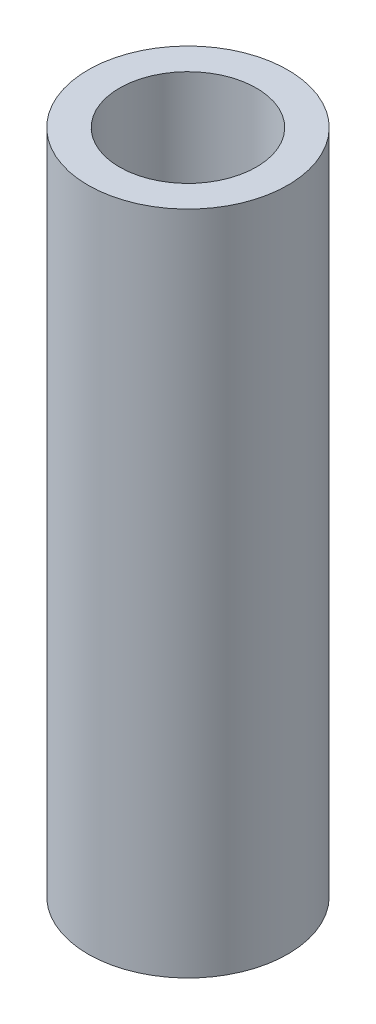
SolidWorks part; units mm, degrees
ref_plane "Front Plane" through (0, 0, 0) normal (0, 0, 1) x (1, 0, 0)
ref_plane "Top Plane" through (0, 0, 0) normal (0, 1, 0) x (1, 0, 0)
ref_plane "Right Plane" through (0, 0, 0) normal (1, 0, 0) x (0, 0, -1)
sketch "Sketch1" plane through (0, 0, 0) normal (0, 1, 0) x (1, 0, 0)
  circle A0 centre (0, 0) radius 2.3812
  dimension "D1" = 4.7625
extrude "Boss-Extrude1" add sketch "Sketch1" along normal blind 15.875
hole_wizard "#4 Clearance Hole1" positions "Sketch3" profile "Sketch2" hole size "#4" standard "Ansi Inch"
sketch "Sketch3" plane through (0, 15.875, 0) normal (0, 1, 0) x (-1, 0, 0)
  circle A0 centre (0, 0) radius 2.3812 construction
  point P0 (0, 0)
sketch "Sketch2" plane through (0, 15.875, 0) normal (1, 0, 0) x (0, 0, 1)
  line L0 (0, 0) -> (0, 8.6006)
  line L1 (0, 8.6006) -> (1.6319, 7.62)
  line L2 (1.6319, 7.62) -> (1.6319, 0)
  line L5 (1.6319, 0) -> (0, 0)
  line L10 (0, 8.6006) -> (-1.632, 7.62) construction
  line L11 (0, -6.35) -> (0, 107.95) construction
  dimension "Hole Dia." = 3.2639
  dimension "Hole Depth" = 7.62
  dimension "Drill Angle" = 118
